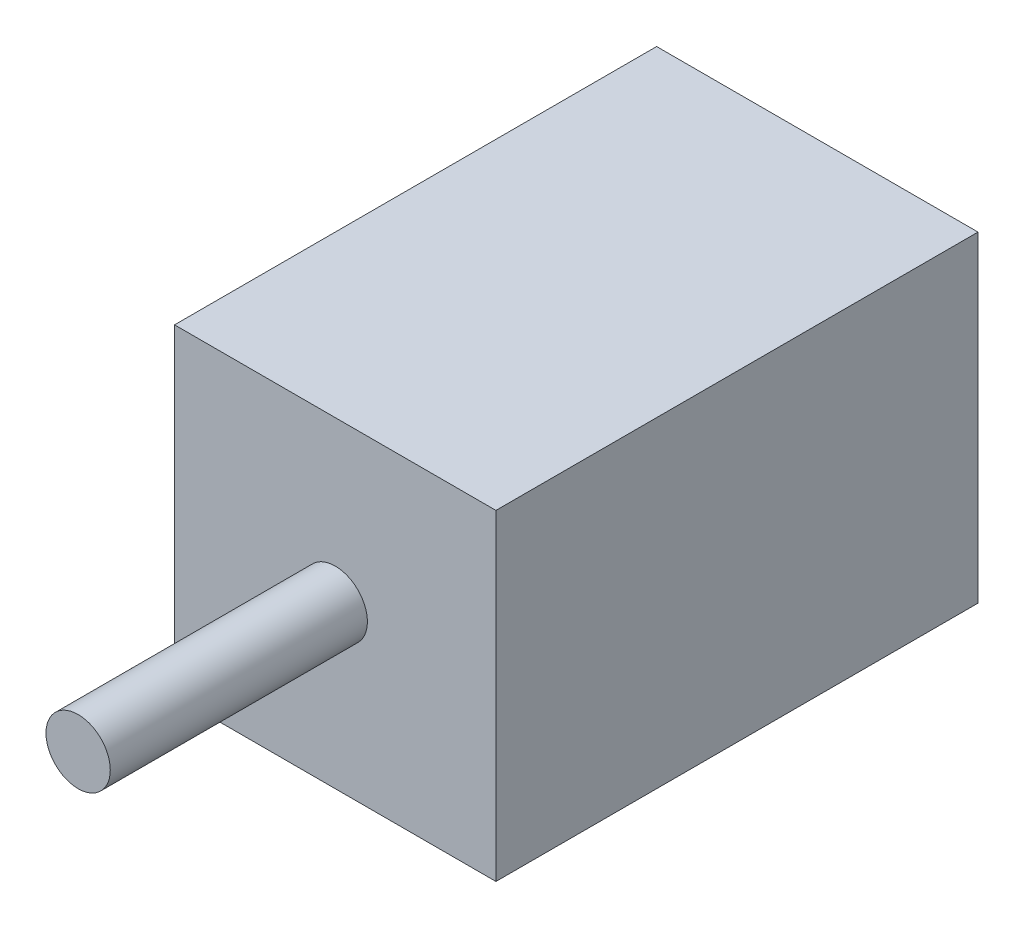
SolidWorks part; units mm, degrees
ref_plane "Ön Düzlem" through (0, 0, 0) normal (0, 0, 1) x (1, 0, 0)
ref_plane "Üst Düzlem" through (0, 0, 0) normal (0, 1, 0) x (1, 0, 0)
ref_plane "Sağ Düzlem" through (0, 0, 0) normal (1, 0, 0) x (0, 0, -1)
sketch "Çizim1" plane through (0, 0, 0) normal (0, 0, 1) x (1, 0, 0)
  line L1 (0, 0) -> (100, 0)
  line L2 (0, 0) -> (0, 100)
  line L3 (0, 100) -> (100, 100)
  line L4 (100, 0) -> (100, 100)
  dimension "D1" = 100
  dimension "D2" = 100
extrude "Yükseklik-Ekstrüzyon1" add sketch "Çizim1" along normal blind 150
sketch "Çizim2" plane through (0, 0, 150) normal (0, 0, 1) x (1, 0, 0)
  circle A0 centre (50, 50) radius 10
  dimension "D1" = 20
extrude "Yükseklik-Ekstrüzyon2" add sketch "Çizim2" along normal blind 80
